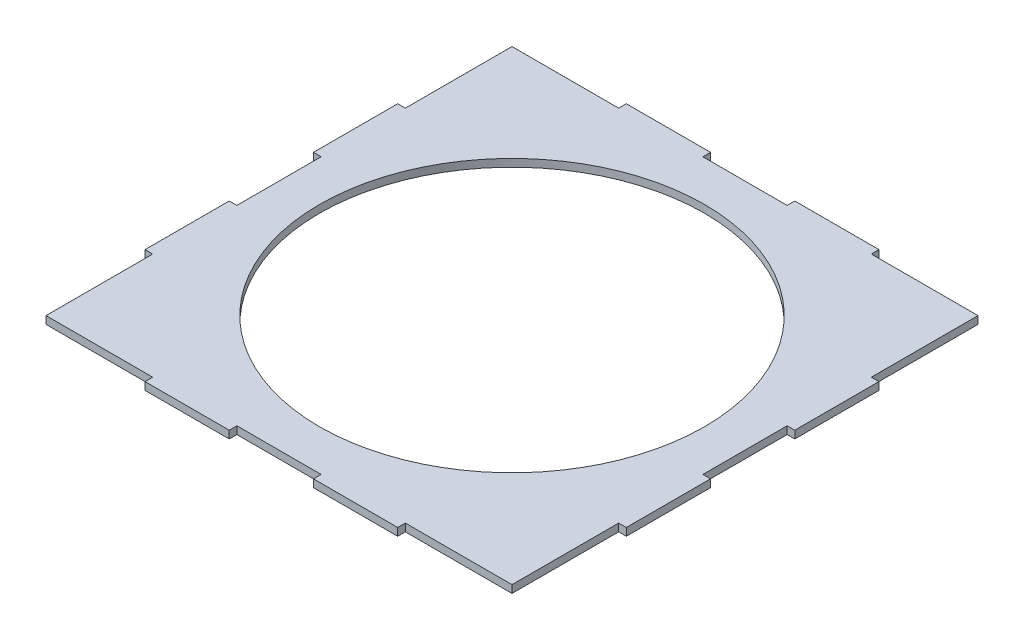
SolidWorks part; units mm, degrees
ref_plane "Plan de face" through (0, 0, 0) normal (0, 0, 1) x (1, 0, 0)
ref_plane "Plan de dessus" through (0, 0, 0) normal (0, 1, 0) x (1, 0, 0)
ref_plane "Plan de droite" through (0, 0, 0) normal (1, 0, 0) x (0, 0, -1)
sketch "Esquisse1" plane through (0, 0, 0) normal (0, 1, 0) x (1, 0, 0)
  line L1 (-100, 100) -> (100, 100)
  line L2 (-100, 100) -> (-100, -100)
  line L3 (-100, -100) -> (100, -100)
  line L4 (100, 100) -> (100, -100)
  point P4 (0, 100)
  point P6 (100, 0)
  dimension "D1" = 200
  dimension "D2" = 200
extrude "Boss.-Extru.1" add sketch "Esquisse1" along normal blind 3.175
sketch "Esquisse2" plane through (0, 3.175, 0) normal (0, 1, 0) x (1, 0, 0)
  line L5 (-100, 100) -> (-100, -100) construction
  line L10 (-100, 17.5) -> (-96.825, 17.5)
  line L11 (-100, 17.5) -> (-100, -17.5)
  line L12 (-100, -17.5) -> (-96.825, -17.5)
  line L13 (-96.825, 17.5) -> (-96.825, -17.5)
  line L15 (-96.825, 52.5) -> (-100, 52.5)
  line L16 (-96.825, 52.5) -> (-96.825, 100)
  line L17 (-96.825, 100) -> (-100, 100)
  line L18 (-100, 52.5) -> (-100, 100)
  line L19 (-100, -100) -> (-96.825, -100)
  line L20 (-100, -100) -> (-100, -52.5)
  line L21 (-100, -52.5) -> (-96.825, -52.5)
  line L22 (-96.825, -100) -> (-96.825, -52.5)
  dimension "D1" = 3.175
  dimension "D2" = 3.175
  dimension "D3" = 3.175
  dimension "D4" = 35
  dimension "D5" = 35
  dimension "D6" = 35
extrude "Enlèv. mat.-Extru.1" cut sketch "Esquisse2" against normal blind 3.175
mirror "Symétrie1" about plane through (0, 0, 0) normal (1, 0, 0) of "Enlèv. mat.-Extru.1"
sketch "Esquisse4" plane through (0, 3.175, 0) normal (0, 1, 0) x (1, 0, 0)
  line L0 (96.825, 100) -> (-96.825, 100) construction
  line L1 (-96.825, 100) -> (-52.5, 100)
  line L2 (-96.825, 100) -> (-96.825, 96.825)
  line L3 (-96.825, 96.825) -> (-52.5, 96.825)
  line L4 (-52.5, 100) -> (-52.5, 96.825)
  line L5 (-17.5, 100) -> (17.5, 100)
  line L6 (-17.5, 100) -> (-17.5, 96.825)
  line L7 (-17.5, 96.825) -> (17.5, 96.825)
  line L8 (17.5, 100) -> (17.5, 96.825)
  line L10 (96.825, 100) -> (52.5, 100)
  line L11 (96.825, 100) -> (96.825, 96.825)
  line L12 (96.825, 96.825) -> (52.5, 96.825)
  line L13 (52.5, 100) -> (52.5, 96.825)
  dimension "D1" = 35
  dimension "D2" = 35
  dimension "D3" = 35
  dimension "D4" = 3.175
  dimension "D5" = 3.175
  dimension "D6" = 3.175
extrude "Enlèv. mat.-Extru.3" cut sketch "Esquisse4" against normal blind 3.175
mirror "Symétrie2" about plane through (0, 0, 0) normal (0, 0, 1) of "Enlèv. mat.-Extru.3"
sketch "Esquisse3" plane through (0, 3.175, 0) normal (0, 1, 0) x (1, 0, 0)
  circle A0 centre (0, 0) radius 80
  dimension "D1" = 160
extrude "Enlèv. mat.-Extru.2" cut sketch "Esquisse3" against normal blind 3.175
